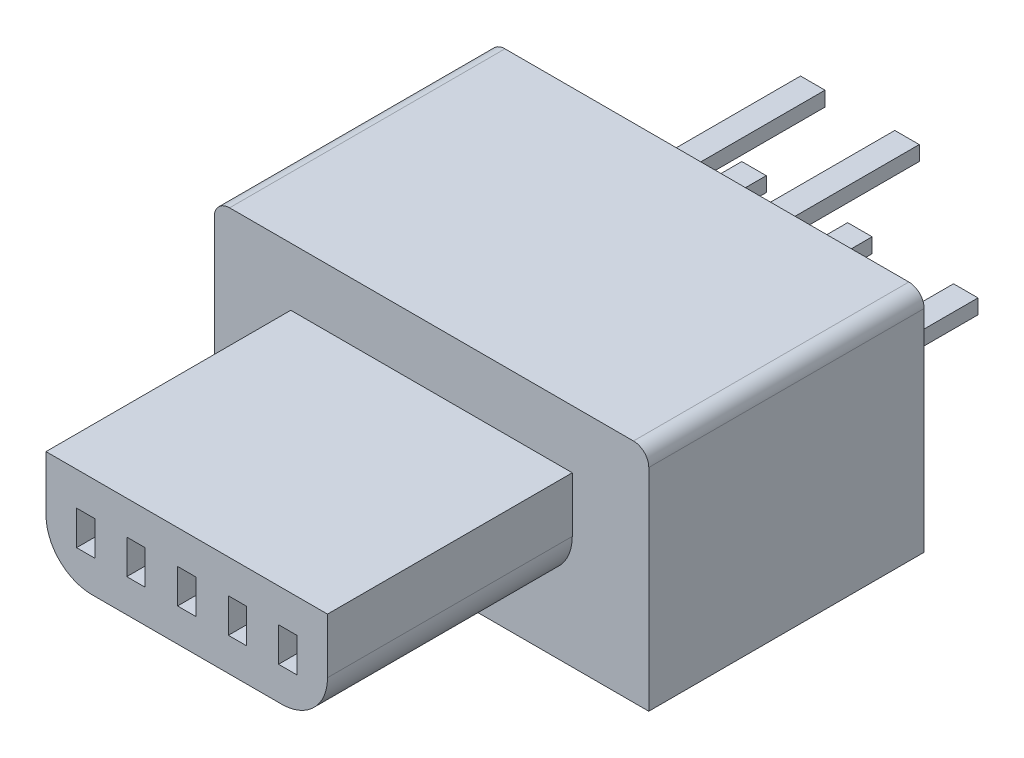
SolidWorks part; units mm, degrees
material "ABS"
ref_plane "Front Plane" through (0, 0, 0) normal (0, 0, 1) x (1, 0, 0)
ref_plane "Top Plane" through (0, 0, 0) normal (0, 1, 0) x (1, 0, 0)
ref_plane "Right Plane" through (0, 0, 0) normal (1, 0, 0) x (0, 0, -1)
sketch "Sketch1" plane through (0, 0, 0) normal (0, 0, 1) x (1, 0, 0)
  line L0 (-4.35, 0.3) -> (2.78, 0.3) construction
  line L1 (3.03, 0.55) -> (3.03, 1.866) construction
  line L2 (3.1372, 2.266) -> (3.483, 2.865) construction
  line L3 (3.55, 3.115) -> (3.55, 3.45) construction
  line L4 (2.3, 2.75) -> (-2.3, 2.75)
  line L5 (-2.3, 2.75) -> (-2.3, 1.85)
  line L6 (-1.55, 1.1) -> (1.55, 1.1)
  line L7 (2.3, 1.85) -> (2.3, 2.75)
  line L8 (2.3, 2.75) -> (-2.3, 2.75)
  line L9 (-2.3, 2.75) -> (-2.3, 1.85)
  line L10 (-1.55, 1.1) -> (1.55, 1.1)
  line L11 (2.3, 1.85) -> (2.3, 2.75)
  line L12 (1.5, 2.2) -> (1.5, 1.64)
  line L13 (1.5, 1.64) -> (1.8, 1.64)
  line L14 (1.8, 1.64) -> (1.8, 2.2)
  line L15 (1.8, 2.2) -> (1.5, 2.2)
  line L16 (1.5, 2.2) -> (1.5, 1.64)
  line L17 (1.5, 1.64) -> (1.8, 1.64)
  line L18 (1.8, 1.64) -> (1.8, 2.2)
  line L19 (1.8, 2.2) -> (1.5, 2.2)
  line L20 (-0.98, 2.2) -> (-0.98, 1.64)
  line L21 (-0.98, 1.64) -> (-0.68, 1.64)
  line L22 (-0.68, 1.64) -> (-0.68, 2.2)
  line L23 (-0.68, 2.2) -> (-0.98, 2.2)
  line L24 (-0.98, 2.2) -> (-0.98, 1.64)
  line L25 (-0.98, 1.64) -> (-0.68, 1.64)
  line L26 (-0.68, 1.64) -> (-0.68, 2.2)
  line L27 (-0.68, 2.2) -> (-0.98, 2.2)
  line L28 (0.15, 1.64) -> (0.15, 2.2)
  line L29 (-0.15, 1.64) -> (0.15, 1.64)
  line L30 (-0.15, 2.2) -> (-0.15, 1.64)
  line L31 (0.15, 2.2) -> (-0.15, 2.2)
  line L32 (0.15, 1.64) -> (0.15, 2.2)
  line L33 (-0.15, 1.64) -> (0.15, 1.64)
  line L34 (-0.15, 2.2) -> (-0.15, 1.64)
  line L35 (0.15, 2.2) -> (-0.15, 2.2)
  line L36 (0.68, 1.64) -> (0.98, 1.64)
  line L37 (0.68, 2.2) -> (0.68, 1.64)
  line L38 (0.98, 2.2) -> (0.68, 2.2)
  line L39 (0.98, 1.64) -> (0.98, 2.2)
  line L40 (0.68, 1.64) -> (0.98, 1.64)
  line L41 (0.68, 2.2) -> (0.68, 1.64)
  line L42 (0.98, 2.2) -> (0.68, 2.2)
  line L43 (0.98, 1.64) -> (0.98, 2.2)
  line L44 (-1.5, 2.2) -> (-1.8, 2.2)
  line L45 (-1.8, 2.2) -> (-1.8, 1.64)
  line L46 (-1.8, 1.64) -> (-1.5, 1.64)
  line L47 (-1.5, 1.64) -> (-1.5, 2.2)
  line L48 (-1.5, 2.2) -> (-1.8, 2.2)
  line L49 (-1.8, 2.2) -> (-1.8, 1.64)
  line L50 (-1.8, 1.64) -> (-1.5, 1.64)
  line L51 (-1.5, 1.64) -> (-1.5, 2.2)
  line L52 (3.3, 3.7) -> (-10.3781, 3.7) construction
  line L53 (-5.9083, 0) -> (2.78, 0) construction
  line L54 (3.33, 0.55) -> (3.33, 1.866) construction
  line L55 (3.397, 2.116) -> (3.7428, 2.715) construction
  line L56 (3.85, 3.115) -> (3.85, 3.45) construction
  line L57 (3.3, 4) -> (-13.106, 4) construction
  line L58 (-4.35, 0.3) -> (2.78, 0.3)
  line L59 (3.03, 0.55) -> (3.03, 1.866)
  line L60 (3.1372, 2.266) -> (3.483, 2.865)
  line L61 (3.55, 3.115) -> (3.55, 3.45)
  line L62 (3.3, 3.7) -> (-10.3781, 3.7)
  line L63 (-5.9083, 0) -> (2.78, 0)
  line L64 (3.33, 0.55) -> (3.33, 1.866)
  line L65 (3.397, 2.116) -> (3.7428, 2.715)
  line L66 (3.85, 3.115) -> (3.85, 3.45)
  line L67 (3.3, 4) -> (-13.106, 4)
  arc A0 (2.78, 0.3) -> (3.03, 0.55) centre (2.78, 0.55) ccw construction
  arc A1 (3.1372, 2.266) -> (3.03, 1.866) centre (3.83, 1.866) ccw construction
  arc A2 (-2.3, 1.85) -> (-1.55, 1.1) centre (-1.55, 1.85) ccw
  arc A3 (1.55, 1.1) -> (2.3, 1.85) centre (1.55, 1.85) ccw
  arc A4 (-2.3, 1.85) -> (-1.55, 1.1) centre (-1.55, 1.85) ccw
  arc A5 (1.55, 1.1) -> (2.3, 1.85) centre (1.55, 1.85) ccw
  arc A6 (3.483, 2.865) -> (3.55, 3.115) centre (3.05, 3.115) ccw construction
  arc A7 (3.55, 3.45) -> (3.3, 3.7) centre (3.3, 3.45) ccw construction
  arc A8 (2.78, 0) -> (3.33, 0.55) centre (2.78, 0.55) ccw construction
  arc A9 (3.397, 2.116) -> (3.33, 1.866) centre (3.83, 1.866) ccw construction
  arc A10 (3.7428, 2.715) -> (3.85, 3.115) centre (3.05, 3.115) ccw construction
  arc A11 (3.85, 3.45) -> (3.3, 4) centre (3.3, 3.45) ccw construction
  arc A12 (2.78, 0.3) -> (3.03, 0.55) centre (2.78, 0.55) ccw
  arc A13 (3.1372, 2.266) -> (3.03, 1.866) centre (3.83, 1.866) ccw
  arc A14 (3.483, 2.865) -> (3.55, 3.115) centre (3.05, 3.115) ccw
  arc A15 (3.55, 3.45) -> (3.3, 3.7) centre (3.3, 3.45) ccw
  arc A16 (2.78, 0) -> (3.33, 0.55) centre (2.78, 0.55) ccw
  arc A17 (3.397, 2.116) -> (3.33, 1.866) centre (3.83, 1.866) ccw
  arc A18 (3.7428, 2.715) -> (3.85, 3.115) centre (3.05, 3.115) ccw
  arc A19 (3.85, 3.45) -> (3.3, 4) centre (3.3, 3.45) ccw
  dimension "D1" = 0
  dimension "D2" = 0
  dimension "D3" = 0
  dimension "D4" = 0
  dimension "D5" = 0
  dimension "D6" = 0
sketch "Sketch2" plane through (0, 0, 0) normal (0, 0, 1) x (1, 0, 0)
  line L0 (2.3, 2.75) -> (-2.3, 2.75) construction
  line L1 (-2.3, 2.75) -> (-2.3, 1.85) construction
  line L2 (-1.55, 1.1) -> (1.55, 1.1) construction
  line L3 (2.3, 1.85) -> (2.3, 2.75) construction
  line L4 (2.3, 2.75) -> (-2.3, 2.75)
  line L5 (-2.3, 2.75) -> (-2.3, 1.85)
  line L6 (-1.55, 1.1) -> (1.55, 1.1)
  line L7 (2.3, 1.85) -> (2.3, 2.75)
  line L8 (-1.8, 1.64) -> (-1.5, 1.64) construction
  line L9 (-1.5, 1.64) -> (-1.5, 2.2) construction
  line L10 (-1.5, 2.2) -> (-1.8, 2.2) construction
  line L11 (-1.8, 2.2) -> (-1.8, 1.64) construction
  line L12 (-1.8, 1.64) -> (-1.5, 1.64)
  line L13 (-1.5, 1.64) -> (-1.5, 2.2)
  line L14 (-1.5, 2.2) -> (-1.8, 2.2)
  line L15 (-1.8, 2.2) -> (-1.8, 1.64)
  line L16 (-0.98, 1.64) -> (-0.68, 1.64) construction
  line L17 (-0.68, 1.64) -> (-0.68, 2.2) construction
  line L18 (-0.68, 2.2) -> (-0.98, 2.2) construction
  line L19 (-0.98, 2.2) -> (-0.98, 1.64) construction
  line L20 (-0.98, 1.64) -> (-0.68, 1.64)
  line L21 (-0.68, 1.64) -> (-0.68, 2.2)
  line L22 (-0.68, 2.2) -> (-0.98, 2.2)
  line L23 (-0.98, 2.2) -> (-0.98, 1.64)
  line L24 (-0.15, 1.64) -> (0.15, 1.64) construction
  line L25 (0.15, 1.64) -> (0.15, 2.2) construction
  line L26 (0.15, 2.2) -> (-0.15, 2.2) construction
  line L27 (-0.15, 2.2) -> (-0.15, 1.64) construction
  line L28 (-0.15, 1.64) -> (0.15, 1.64)
  line L29 (0.15, 1.64) -> (0.15, 2.2)
  line L30 (0.15, 2.2) -> (-0.15, 2.2)
  line L31 (-0.15, 2.2) -> (-0.15, 1.64)
  line L32 (0.68, 1.64) -> (0.98, 1.64) construction
  line L33 (0.98, 1.64) -> (0.98, 2.2) construction
  line L34 (0.98, 2.2) -> (0.68, 2.2) construction
  line L35 (0.68, 2.2) -> (0.68, 1.64) construction
  line L36 (0.68, 1.64) -> (0.98, 1.64)
  line L37 (0.98, 1.64) -> (0.98, 2.2)
  line L38 (0.98, 2.2) -> (0.68, 2.2)
  line L39 (0.68, 2.2) -> (0.68, 1.64)
  line L40 (1.5, 1.64) -> (1.8, 1.64) construction
  line L41 (1.8, 1.64) -> (1.8, 2.2) construction
  line L42 (1.8, 2.2) -> (1.5, 2.2) construction
  line L43 (1.5, 2.2) -> (1.5, 1.64) construction
  line L44 (1.5, 1.64) -> (1.8, 1.64)
  line L45 (1.8, 1.64) -> (1.8, 2.2)
  line L46 (1.8, 2.2) -> (1.5, 2.2)
  line L47 (1.5, 2.2) -> (1.5, 1.64)
  arc A0 (-2.3, 1.85) -> (-1.55, 1.1) centre (-1.55, 1.85) ccw construction
  arc A1 (1.55, 1.1) -> (2.3, 1.85) centre (1.55, 1.85) ccw construction
  arc A2 (-2.3, 1.85) -> (-1.55, 1.1) centre (-1.55, 1.85) ccw
  arc A3 (1.55, 1.1) -> (2.3, 1.85) centre (1.55, 1.85) ccw
extrude "Boss-Extrude1" add sketch "Sketch2" against normal blind 4 from offset 0.9 offset against normal yes
sketch "Sketch3" plane through (0, 0, -4.9) normal (0, 0, -1) x (-1, 0, 0)
  line L0 (-3.3, 3.7) -> (10.3781, 3.7) construction
  line L1 (-3.3, 3.7) -> (3.3, 3.7)
  line L2 (5.9083, 0) -> (-2.78, 0) construction
  line L3 (3.55, 0) -> (-3.55, 0)
  line L4 (-3.55, 3.115) -> (-3.55, 3.45) construction
  line L5 (-3.55, 0) -> (-3.55, 3.45)
  line L6 (0, 0) -> (0, 4.4133) construction
  line L10 (3.55, 0) -> (3.55, 3.45)
  arc A0 (-3.3, 3.7) -> (-3.55, 3.45) centre (-3.3, 3.45) ccw construction
  arc A1 (-3.3, 3.7) -> (-3.55, 3.45) centre (-3.3, 3.45) ccw
  arc A3 (3.3, 3.7) -> (3.55, 3.45) centre (3.3, 3.45) cw
extrude "Boss-Extrude2" add sketch "Sketch3" along normal blind 4.5
sketch "Sketch4" plane through (0, 0, -9.4) normal (0, 0, -1) x (-1, 0, 0)
  line L0 (0, 0) -> (0, 4.1279) construction
  line L1 (-3.55, 0) -> (3.55, 0) construction
  line L2 (-0.57, 3.23) -> (-0.57, 2.99)
  line L3 (0.57, 3.23) -> (0.97, 3.23)
  line L4 (0.57, 3.23) -> (0.57, 2.99)
  line L5 (0.57, 2.99) -> (0.97, 2.99)
  line L6 (0.97, 3.23) -> (0.97, 2.99)
  line L7 (-0.2, 1.54) -> (0.2, 1.54)
  line L8 (-0.2, 1.54) -> (-0.2, 1.3)
  line L9 (-0.2, 1.3) -> (0.2, 1.3)
  line L10 (0.2, 1.54) -> (0.2, 1.3)
  line L11 (1.53, 1.54) -> (1.93, 1.54)
  line L12 (1.53, 1.54) -> (1.53, 1.3)
  line L13 (1.53, 1.3) -> (1.93, 1.3)
  line L14 (1.93, 1.54) -> (1.93, 1.3)
  line L15 (-0.57, 3.23) -> (-0.97, 3.23)
  line L16 (-0.97, 3.23) -> (-0.97, 2.99)
  line L17 (-0.57, 2.99) -> (-0.97, 2.99)
  line L18 (-1.53, 1.3) -> (-1.93, 1.3)
  line L19 (-1.93, 1.54) -> (-1.93, 1.3)
  line L20 (-1.53, 1.54) -> (-1.93, 1.54)
  line L21 (-1.53, 1.54) -> (-1.53, 1.3)
  dimension "D1" = 0.24
  dimension "D2" = 0.4
  dimension "D3" = 1.94
  dimension "D4" = 3.86
  dimension "D5" = 1.3
  dimension "D6" = 1.93
extrude "Boss-Extrude3" add sketch "Sketch4" along normal blind 2.5
